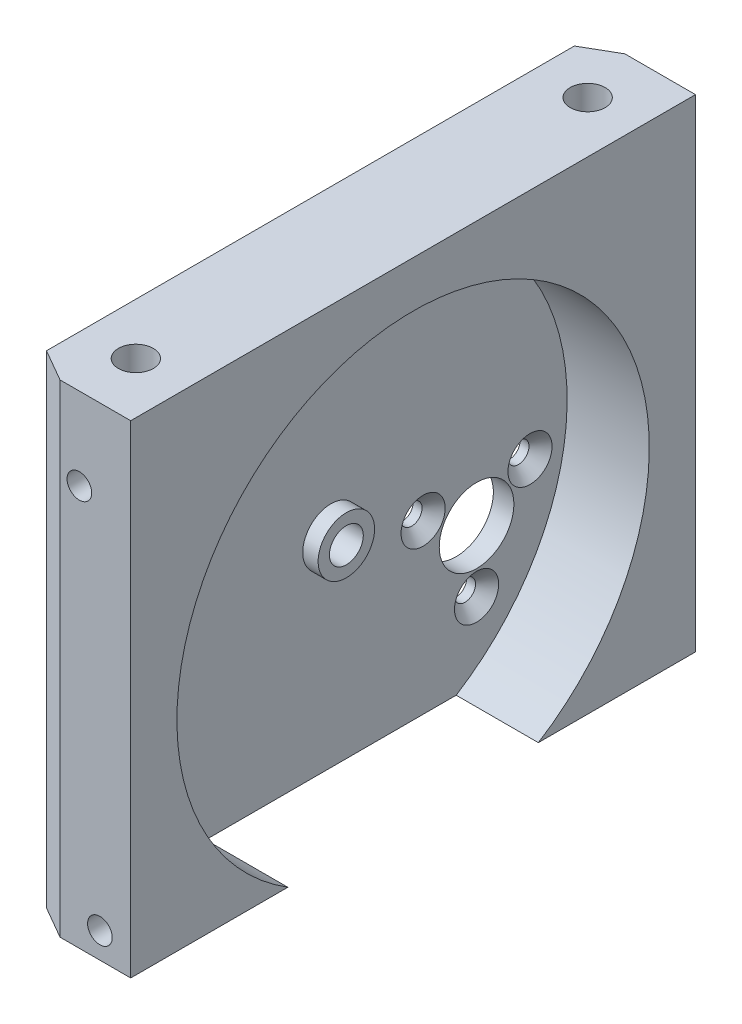
SolidWorks part; units mm, degrees
ref_plane "Front Plane" through (0, 0, 0) normal (0, 0, 1) x (1, 0, 0)
ref_plane "Top Plane" through (0, 0, 0) normal (0, 1, 0) x (1, 0, 0)
ref_plane "Right Plane" through (0, 0, 0) normal (1, 0, 0) x (0, 0, -1)
sketch "Sketch1" plane through (0, 0, 0) normal (1, 0, 0) x (0, 0, -1)
  line L1 (-42.1813, 33.1255) -> (12.8187, 33.1255)
  line L2 (-42.1813, 33.1255) -> (-42.1813, -13.8745)
  line L3 (-42.1813, -13.8745) -> (12.8187, -13.8745)
  line L4 (12.8187, 33.1255) -> (12.8187, -13.8745)
  dimension "D1" = 55
  dimension "D2" = 47
extrude "Extrude1" add sketch "Sketch1" along normal blind 10
sketch "Sketch2" plane through (10, 0, 0) normal (1, 0, 0) x (0, 0, -1)
  line L0 (-42.1813, -13.8745) -> (12.8187, -13.8745) construction
  line L1 (12.8187, -13.8745) -> (12.8187, 33.1255) construction
  circle A0 centre (-14.6813, 5.6255) radius 23
  dimension "D1" = 46
  dimension "D3" = 27.5
  dimension "D2" = 19.5
extrude "Extrude2" cut sketch "Sketch2" against normal blind 8
sketch "Sketch3" plane through (0, 0, 42.1813) normal (0, 0, 1) x (1, 0, 0)
  line L0 (10, 33.1255) -> (0, 33.1255) construction
  line L1 (10, 33.1255) -> (10, -13.8745) construction
  line L3 (10, -13.8745) -> (0, -13.8745) construction
  circle A0 centre (5, 25.1255) radius 1.2
  circle A1 centre (7, -11.3745) radius 1.2
  dimension "D1" = 2.4
  dimension "D3" = 5
  dimension "D4" = 2.4
  dimension "D5" = 2.5
  dimension "D6" = 3
  dimension "D2" = 8
extrude "Extrude3" cut sketch "Sketch3" against normal blind 6
sketch "Sketch4" plane through (0, 0, -12.8187) normal (0, 0, -1) x (-1, 0, 0)
  line L1 (-10, 33.1255) -> (0, 33.1255) construction
  line L2 (-10, -13.8745) -> (0, -13.8745) construction
  line L3 (-10, -13.8745) -> (-10, 33.1255) construction
  circle A0 centre (-5, 25.1255) radius 1.2
  circle A1 centre (-7, -11.3745) radius 1.2
  dimension "D1" = 2.4
  dimension "D2" = 2.4
  dimension "D3" = 5
  dimension "D4" = 3
  dimension "D5" = 8
  dimension "D6" = 2.5
extrude "Extrude4" cut sketch "Sketch4" against normal blind 6
sketch "Sketch5" plane through (2, 0, 0) normal (1, 0, 0) x (0, 0, -1)
  circle A0 centre (-14.6813, 5.6255) radius 1.65
  circle A1 centre (-14.6813, 5.6255) radius 2.75
  dimension "D1" = 3.3
  dimension "D2" = 5.5
extrude "Extrude5" add sketch "Sketch5" along normal blind 1.5
sketch "Sketch6" plane through (2, 0, 0) normal (1, 0, 0) x (0, 0, -1)
  circle A0 centre (-14.6813, 5.6255) radius 1.65
  dimension "D1" = 3.3
extrude "Extrude6" cut sketch "Sketch6" against normal blind 2
sketch "Sketch7" plane through (0, 0, 0) normal (-1, 0, 0) x (0, 0, 1)
  line L0 (42.1813, -13.8745) -> (-12.8187, -13.8745) construction
  line L1 (-12.8187, -13.8745) -> (-12.8187, 33.1255) construction
  circle A0 centre (0.5013, -0.5545) radius 3.635
  dimension "D1" = 13.32
  dimension "D2" = 13.32
  dimension "D3" = 7.27
extrude "Extrude7" cut sketch "Sketch7" against normal blind 3
hole_wizard "CSK for M1.6 Countersunk Flat Head Screw1" positions "3DSketch3" profile "Sketch10" countersink size "M1.6" standard "ISO" end condition through all
sketch3d "3DSketch3"
  point P0 (2, 2.4505, 5.7063)
  point P2 (2, 2.4505, -4.7037)
  point P4 (2, -6.5645, 0.5013)
  dimension "D1" = 13.32
  dimension "D2" = 7.31
  dimension "D3" = 16.325
  dimension "D4" = 8.115
  dimension "D5" = 18.525
  dimension "D6" = 16.325
sketch "Sketch10" plane through (2, 2.4505, 5.7063) normal (0, 1, 0) x (0, 0, -1)
  line L0 (0, 0) -> (0, 2)
  line L1 (0, 2) -> (1.025, 2)
  line L2 (1.025, 2) -> (1.025, 1.125)
  line L3 (1.025, 1.125) -> (2.15, 0)
  line L5 (2.15, 0) -> (0, 0)
  line L6 (-1.025, 1.125) -> (-2.15, 0) construction
  line L11 (0, -6.35) -> (0, 107.95) construction
  dimension "Thru Hole Dia." = 2.05
  dimension "Thru Hole Depth" = 2
  dimension "Near C'Sink Dia." = 4.3
  dimension "Near C'Sink Angle" = 90
chamfer "Chamfer1" distance 1.8 angle 60 2 edges at (0, 9.6255, 42.1813) (0, 9.6255, -12.8187)
hole_wizard "Ø3.4 (3.4) Diameter Hole1" positions "3DSketch4" profile "Sketch11" hole size "Ø3.4" standard "Ansi Metric"
sketch3d "3DSketch4"
  point P0 (5, 33.1255, -7.3187)
  point P2 (5, 33.1255, 36.6813)
  dimension "D1" = 5
  dimension "D2" = 5.5
  dimension "D3" = 5
  dimension "D4" = 5.5
sketch "Sketch11" plane through (5, 33.1255, -7.3187) normal (1, 0, 0) x (0, 0, 1)
  line L0 (0, 0) -> (0, 5.0215)
  line L1 (0, 5.0215) -> (1.7, 4)
  line L2 (1.7, 4) -> (1.7, 0)
  line L5 (1.7, 0) -> (0, 0)
  line L10 (0, 5.0215) -> (-1.7, 4) construction
  line L11 (0, -6.35) -> (0, 107.95) construction
  dimension "Hole Dia." = 3.4
  dimension "Hole Depth" = 4
  dimension "Drill Angle" = 118
